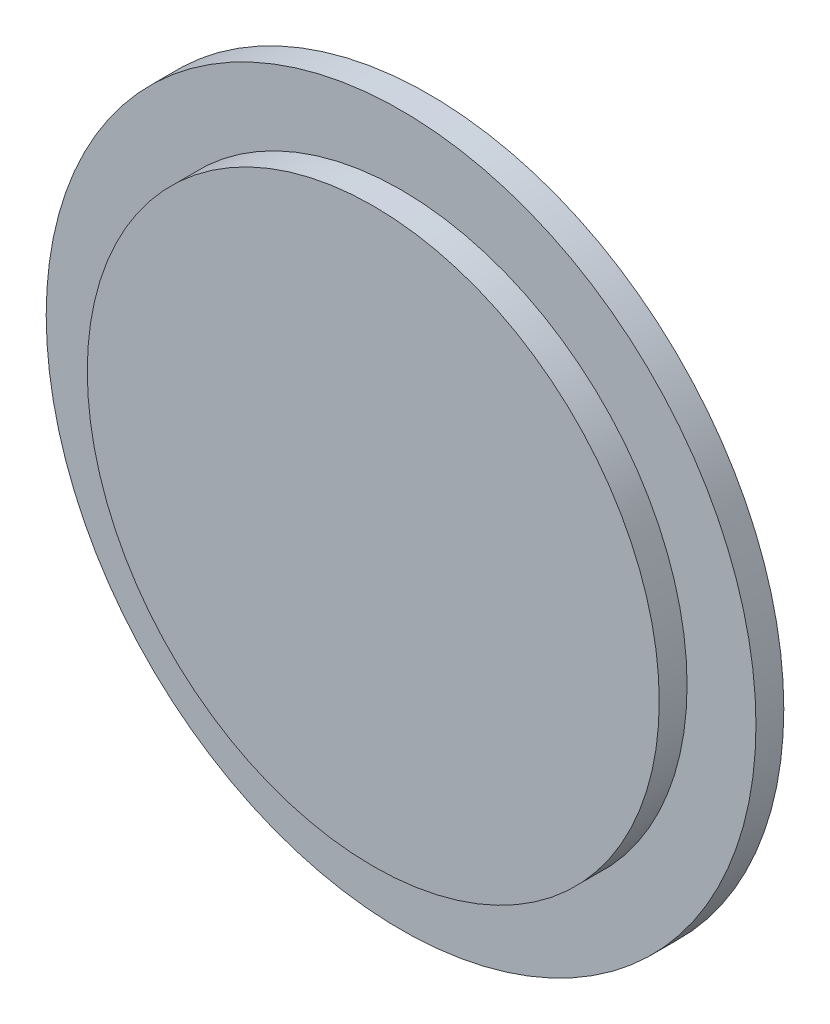
SolidWorks part; units mm, degrees
ref_plane "Front" through (0, 0, 0) normal (0, 0, 1) x (1, 0, 0)
ref_plane "Top" through (0, 0, 0) normal (0, 1, 0) x (1, 0, 0)
ref_plane "Right" through (0, 0, 0) normal (1, 0, 0) x (0, 0, -1)
sketch "Sketch1" plane through (0, 0, 0) normal (0, 0, 1) x (1, 0, 0)
  circle A0 centre (0, 0) radius 25.5
  dimension "D1" = 51
extrude "Boss-Extrude1" add sketch "Sketch1" along normal blind 2
sketch "Sketch2" plane through (0, 0, 2) normal (0, 0, 1) x (1, 0, 0)
  circle A0 centre (0, 0) radius 20.55
  circle A1 centre (0, 0) radius 25.5 construction
  dimension "D1" = 4.95
extrude "Boss-Extrude2" add sketch "Sketch2" along normal blind 2 contours A0
